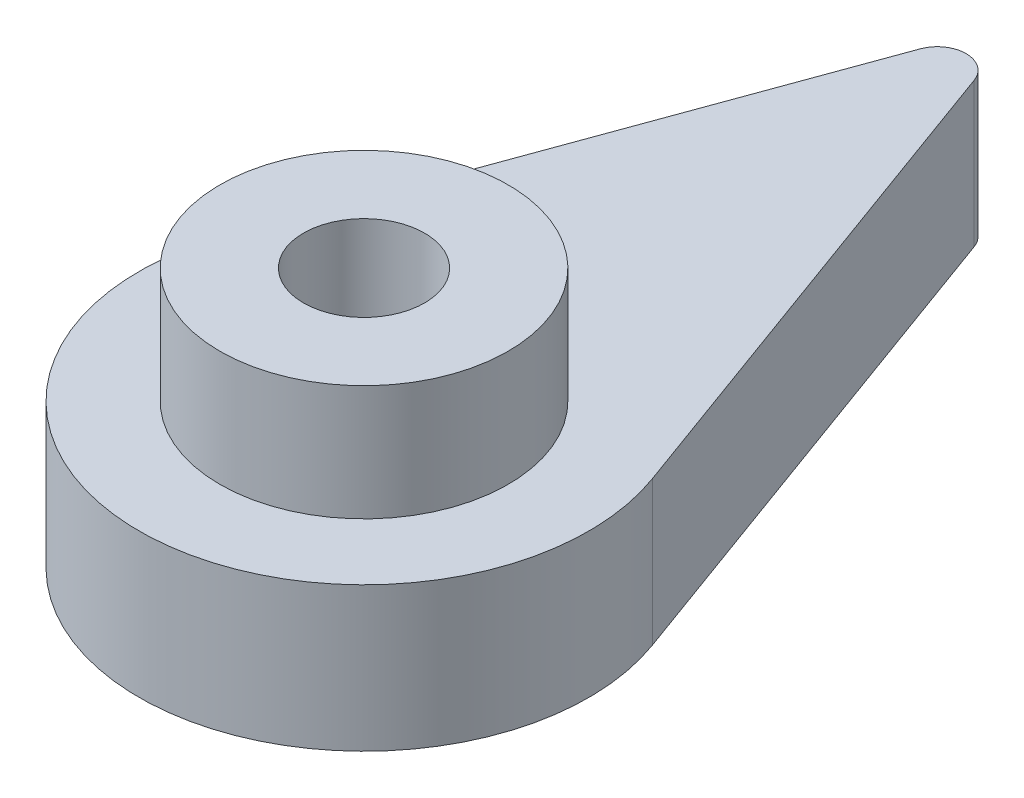
SolidWorks part; units mm, degrees
ref_plane "Front Plane" through (0, 0, 0) normal (0, 0, 1) x (1, 0, 0)
ref_plane "Top Plane" through (0, 0, 0) normal (0, 1, 0) x (1, 0, 0)
ref_plane "Right Plane" through (0, 0, 0) normal (1, 0, 0) x (0, 0, -1)
sketch "Sketch1" plane through (0, 0, 0) normal (0, 1, 0) x (1, 0, 0)
  line L3 (0, -55) -> (0, 55) construction
  line L12 (-0.9397, 20.2239) -> (-7.3296, 2.6678)
  line L15 (7.3296, 2.6678) -> (0.9397, 20.2239)
  arc A0 (-7.3296, 2.6678) -> (7.3296, 2.6678) centre (0, 0) ccw
  arc A12 (0.9397, 20.2239) -> (-0.9397, 20.2239) centre (0, 19.8819) ccw
  dimension "D1" = 7.8
  dimension "D3" = 1
  dimension "D5" = 40
extrude "Boss-Extrude2" add sketch "Sketch1" along normal blind 5
sketch "Sketch3" plane through (0, 5, 0) normal (0, 1, 0) x (1, 0, 0)
  circle A0 centre (0, 0) radius 2.1
  dimension "D1" = 4.2
extrude "Cut-Extrude1" cut sketch "Sketch3" against normal up to next
sketch "Sketch5" plane through (0, 0, 0) normal (0, -1, 0) x (1, 0, 0)
  line L0 (0, -2.75) -> (0, 2.75) construction
  line L1 (0, 4.2724) -> (-3.7, 2.1362)
  line L2 (-3.7, 2.1362) -> (-3.7, -2.1362)
  line L3 (-3.7, -2.1362) -> (0, -4.2724)
  line L4 (0, -4.2724) -> (3.7, -2.1362)
  line L5 (3.7, -2.1362) -> (3.7, 2.1362)
  line L6 (3.7, 2.1362) -> (0, 4.2724)
  circle A0 centre (0, 0) radius 3.7 construction
  dimension "D1" = 7.4
extrude "Cut-Extrude3" cut sketch "Sketch5" against normal blind 1.8
sketch "Sketch6" plane through (0, 5, 0) normal (0, 1, 0) x (1, 0, 0)
  circle A0 centre (0, 0) radius 5
  circle A1 centre (0, 0) radius 2.1
  circle A2 centre (0, 0) radius 2.1 construction
  dimension "D1" = 10
extrude "Boss-Extrude3" add sketch "Sketch6" along normal blind 4
